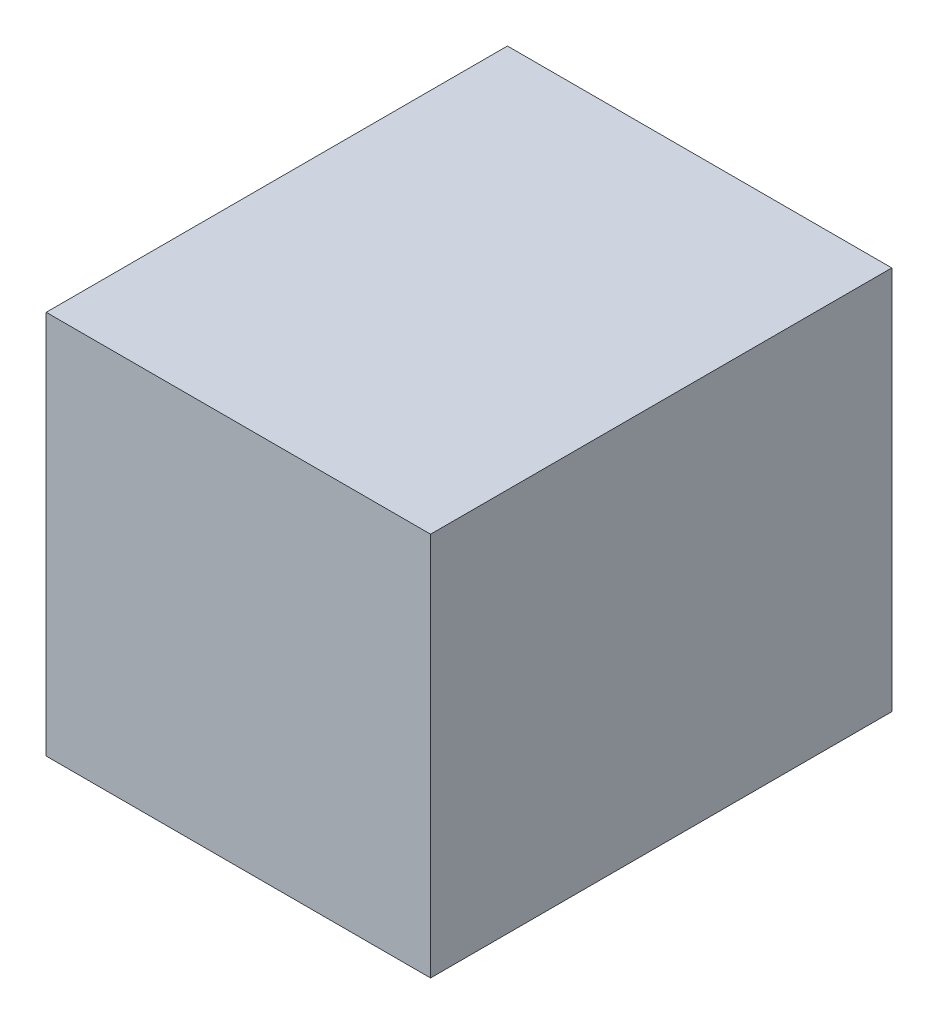
SolidWorks part; units mm, degrees
ref_plane "Front Plane" through (0, 0, 0) normal (0, 0, 1) x (1, 0, 0)
ref_plane "Top Plane" through (0, 0, 0) normal (0, 1, 0) x (1, 0, 0)
ref_plane "Right Plane" through (0, 0, 0) normal (1, 0, 0) x (0, 0, -1)
sketch "Sketch1" plane through (0, 0, 0) normal (0, 0, 1) x (1, 0, 0)
  line L1 (-2.5, -2.5) -> (2.5, -2.5)
  line L2 (-2.5, -2.5) -> (-2.5, 2.5)
  line L3 (-2.5, 2.5) -> (2.5, 2.5)
  line L4 (2.5, -2.5) -> (2.5, 2.5)
  line L5 (-2.5, -2.5) -> (2.5, 2.5) construction
  line L6 (-2.5, 2.5) -> (2.5, -2.5) construction
  point P0 (0, 0)
  dimension "D1" = 5
  dimension "D2" = 5
extrude "Boss-Extrude1" add sketch "Sketch1" along normal mid plane 6
